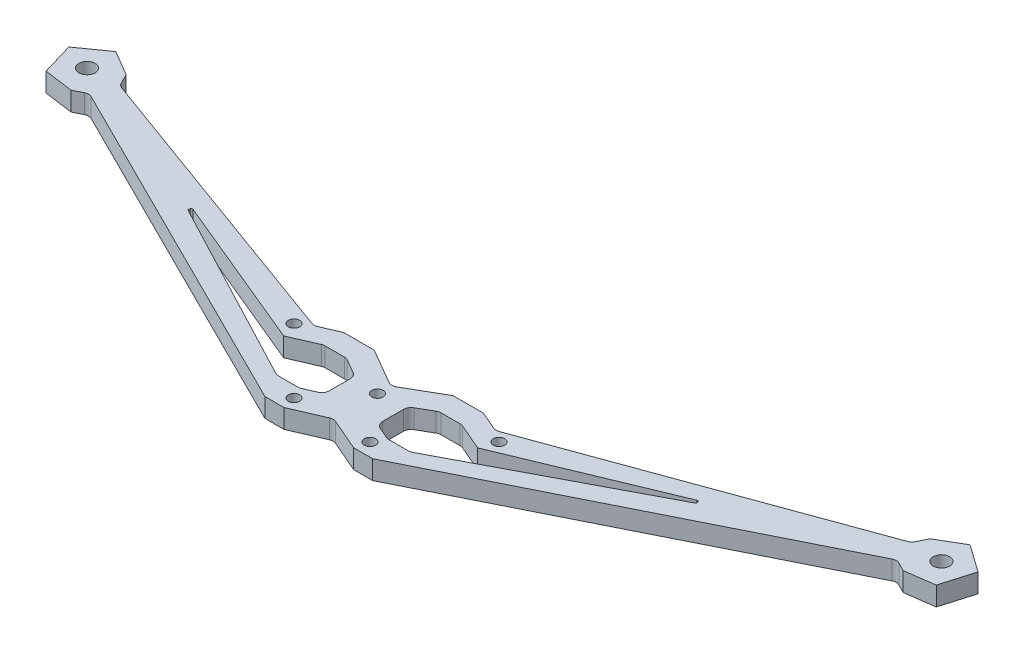
SolidWorks part; units mm, degrees
material "自定义塑料"
ref_plane "前视基准面" through (0, 0, 0) normal (0, 0, 1) x (1, 0, 0)
ref_plane "上视基准面" through (0, 0, 0) normal (0, 1, 0) x (1, 0, 0)
ref_plane "右视基准面" through (0, 0, 0) normal (1, 0, 0) x (0, 0, -1)
sketch "草图1" plane through (0, 0, 0) normal (0, 1, 0) x (1, 0, 0)
  line L0 (0, 0) -> (-112.5, 0)
  line L1 (-112.5, 0) -> (-112.5, 159.336)
  line L2 (0, 0) -> (112.5, 0)
  line L3 (112.5, 0) -> (112.5, 164.4426)
sketch "草图2" plane through (0, 0, 0) normal (0, 1, 0) x (1, 0, 0)
  line L0 (0, -7.5) -> (0, 7.5)
  line L1 (0, -7.5) -> (-9.1773, -11.4719)
  line L2 (0, 7.5) -> (-10.3923, 13.5)
  line L3 (-10.3923, 13.5) -> (-18.3923, 13.5)
  line L4 (-18.3923, 13.5) -> (-23.8987, 11.1168)
  line L5 (-23.8987, 11.1168) -> (-104.2164, 40.3501)
  line L6 (0, 0) -> (80.833, 0) construction
  line L7 (0, 0) -> (112.5, 0) construction
  line L12 (-9.1773, -11.4719) -> (-14.1773, -11.4719)
  line L13 (-14.1773, -11.4719) -> (-103.3239, 32.9749)
  line L14 (-104.2164, 40.3501) -> (-106.3513, 34.4843)
  line L15 (-103.3239, 32.9749) -> (-106.3513, 34.4843)
  point P4 (0, 0)
extrude "凸台-拉伸1" add sketch "草图2" along normal blind 5
sketch "草图4" plane through (0, 0, 0) normal (0, 1, 0) x (1, 0, 0)
  line L0 (-105.2838, 37.4172) -> (-119.0674, 42.1963)
  line L2 (-104.2164, 40.3501) -> (-106.3513, 34.4843) construction
  line L3 (-112.5, 0) -> (-112.5, 159.336) construction
  line L11 (-112.5, 39.9192) -> (-105.8365, 43.6517)
  line L12 (-105.8365, 43.6517) -> (-104.2164, 40.3501)
  line L13 (-105.8365, 43.6517) -> (-112.5, 47.5569)
  line L14 (-119.0674, 42.1963) -> (-121.7053, 43.111)
  line L15 (-112.5, 47.5569) -> (-119.7162, 42.4213)
  line L16 (-109.5773, 32.863) -> (-117.228, 33.9209)
  line L17 (-117.228, 33.9209) -> (-119.7162, 42.4213)
  line L18 (-109.5773, 32.863) -> (-106.3513, 34.4843)
  line L19 (-104.2164, 40.3501) -> (-106.3513, 34.4843)
  circle A0 centre (-112.5, 39.9192) radius 7.6376
  point P4 (-112.5, 39.9192)
extrude "凸台-拉伸2" add sketch "草图4" along normal blind 5 contours L12 L19 L18 L16 L17 L15 L13
sketch "草图5" plane through (0, 5, 0) normal (0, 1, 0) x (1, 0, 0)
  line L0 (-112.5, 0) -> (-112.5, 40)
  line L1 (-112.5, 0) -> (-112.5, 159.336) construction
  circle A0 centre (-112.5, 40) radius 2.15
extrude "切除-拉伸3" cut sketch "草图5" against normal blind 3.5
sketch "草图6" plane through (0, 5, 0) normal (0, 1, 0) x (1, 0, 0)
  line L0 (-64.6687, 25.9559) -> (-69.5166, 16.1192)
  line L1 (-23.8987, 11.1168) -> (-104.2164, 40.3501) construction
  line L2 (-106.3513, 34.4843) -> (-14.1773, -11.4719) construction
  line L3 (0, 0) -> (-7, 0)
  line L4 (0, 0) -> (-112.5, 0) construction
  line L5 (-7, 0) -> (-7, 5)
  line L6 (-7, 5) -> (-12.1962, 8)
  line L7 (-12.1962, 8) -> (-18.1962, 8)
  line L8 (-18.1962, 8) -> (-25.538, 4.8224)
  line L10 (-7, 0) -> (-7, -3)
  line L11 (-7, -3) -> (-11.5887, -4.986)
  line L12 (-11.5887, -4.986) -> (-17.5887, -4.986)
  line L13 (-17.5887, -4.986) -> (-67.0926, 21.0375)
  line L14 (0, 7.5) -> (-10.3923, 13.5) construction
  line L15 (-25.538, 4.8224) -> (-66.6707, 21.8936)
  line L16 (-9.1773, -11.4719) -> (0, -7.5) construction
  line L17 (-18.3923, 13.5) -> (-23.8987, 11.1168) construction
extrude "切除-拉伸4" cut sketch "草图6" against normal blind 5
sketch "草图8" plane through (0, 5, 0) normal (0, 1, 0) x (1, 0, 0)
  line L0 (0, 0) -> (-7, 0)
  line L1 (0, -7.5) -> (0, 7.5) construction
  line L2 (0, 0) -> (-112.5, 0) construction
  line L3 (-7, 5) -> (-7, -3) construction
  line L5 (-7, 0) -> (-10, 0)
  line L6 (-10, 0) -> (-10, -8)
  circle A0 centre (0, 4) radius 1.5
  circle A1 centre (-10, -8) radius 1.5
  circle A2 centre (-27, 9) radius 1.5
extrude "切除-拉伸5" cut sketch "草图8" against normal blind 5
fillet "圆角1" radius 2 7 edges at (-7, 2.5, 3) (-7, 2.5, -5) (-12.1962, 2.5, -8) (-18.1962, 2.5, -8) (-23.8987, 2.5, -11.1168) (-17.5887, 2.5, 4.986) (-11.5887, 2.5, 4.986)
fillet "圆角2" radius 0.4 2 edges at (-67.0926, 2.5, -21.0375) (-66.6707, 2.5, -21.8936)
fillet "圆角4" radius 2 2 edges at (-104.2164, 2.5, -40.3501) (-106.3513, 2.5, -34.4843)
mirror "镜向2" of "圆角4", "切除-拉伸5", "切除-拉伸4", "凸台-拉伸2", "切除-拉伸3", "凸台-拉伸1", "圆角1", "圆角2"
fillet "圆角3" radius 2 2 edges at (0, 2.5, 7.5) (0, 2.5, -7.5)
sketch "草图9" plane through (0, 0, 0) normal (0, -1, 0) x (1, 0, 0)
  line L1 (-6.8246, 8) -> (-8.4123, 10.75)
  line L2 (-8.4123, 10.75) -> (-11.5877, 10.75)
  line L3 (-11.5877, 10.75) -> (-13.1754, 8)
  line L4 (-13.1754, 8) -> (-11.5877, 5.25)
  line L5 (-11.5877, 5.25) -> (-8.4123, 5.25)
  line L6 (-8.4123, 5.25) -> (-6.8246, 8)
  line L7 (3.1754, -4) -> (1.5877, -1.25)
  line L8 (1.5877, -1.25) -> (-1.5877, -1.25)
  line L9 (-1.5877, -1.25) -> (-3.1754, -4)
  line L10 (-3.1754, -4) -> (-1.5877, -6.75)
  line L11 (-1.5877, -6.75) -> (1.5877, -6.75)
  line L12 (1.5877, -6.75) -> (3.1754, -4)
  line L13 (13.1754, 8) -> (11.5877, 10.75)
  line L14 (11.5877, 10.75) -> (8.4123, 10.75)
  line L15 (8.4123, 10.75) -> (6.8246, 8)
  line L16 (6.8246, 8) -> (8.4123, 5.25)
  line L17 (8.4123, 5.25) -> (11.5877, 5.25)
  line L18 (11.5877, 5.25) -> (13.1754, 8)
  line L19 (-109.3246, -40) -> (-110.9123, -37.25)
  line L20 (-110.9123, -37.25) -> (-114.0877, -37.25)
  line L21 (-114.0877, -37.25) -> (-115.6754, -40)
  line L22 (-115.6754, -40) -> (-114.0877, -42.75)
  line L23 (-114.0877, -42.75) -> (-110.9123, -42.75)
  line L24 (-110.9123, -42.75) -> (-109.3246, -40)
  line L25 (115.6754, -40) -> (114.0877, -37.25)
  line L26 (114.0877, -37.25) -> (110.9123, -37.25)
  line L27 (110.9123, -37.25) -> (109.3246, -40)
  line L28 (109.3246, -40) -> (110.9123, -42.75)
  line L29 (110.9123, -42.75) -> (114.0877, -42.75)
  line L30 (114.0877, -42.75) -> (115.6754, -40)
  circle A0 centre (-10, 8) radius 2.75 construction
  circle A1 centre (0, -4) radius 2.75 construction
  circle A2 centre (10, 8) radius 2.75 construction
  circle A3 centre (-112.5, -40) radius 2.75 construction
  circle A4 centre (112.5, -40) radius 2.75 construction
sketch "草图10" plane through (0, 1.5, 0) normal (0, 1, 0) x (1, 0, 0)
  circle A0 centre (-112.5, 40) radius 0.8
  circle A1 centre (112.5, 40) radius 0.8
extrude "切除-拉伸6" cut sketch "草图10" against normal blind 10
